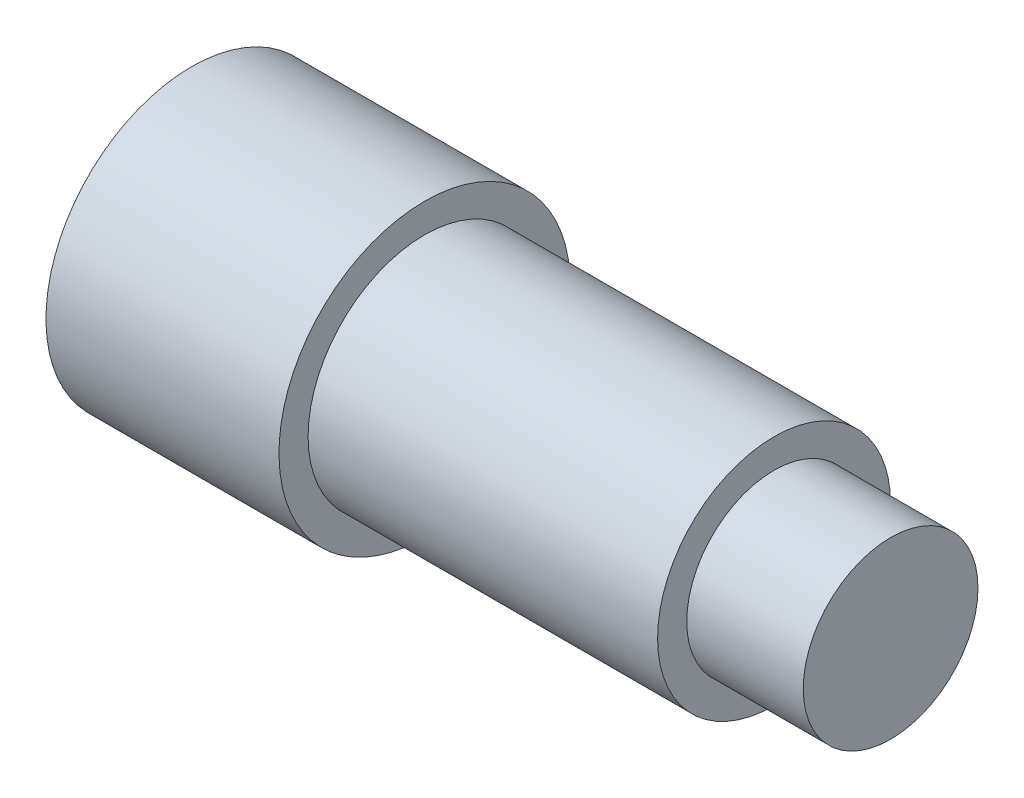
SolidWorks part; units mm, degrees
ref_plane "Face" through (0, 0, 0) normal (0, 0, 1) x (1, 0, 0)
ref_plane "Dessus" through (0, 0, 0) normal (0, 1, 0) x (1, 0, 0)
ref_plane "Droite" through (0, 0, 0) normal (1, 0, 0) x (0, 0, -1)
sketch "Esquisse1" plane through (0, 0, 0) normal (0, 0, 1) x (1, 0, 0)
  line L0 (0, 0) -> (0, 2.5)
  line L1 (0, 2.5) -> (4, 2.5)
  line L2 (4, 2.5) -> (4, 2)
  line L3 (4, 2) -> (10, 2)
  line L4 (10, 2) -> (10, 1.5)
  line L5 (10, 1.5) -> (12, 1.5)
  line L6 (12, 1.5) -> (12, 0)
  line L7 (12, 0) -> (0, 0)
  dimension "D1" = 2.5
  dimension "D2" = 1.5
  dimension "D3" = 2
  dimension "D4" = 4
  dimension "D5" = 6
  dimension "D6" = 12
revolve "Révolution1" add sketch "Esquisse1" angle 360 about L7
